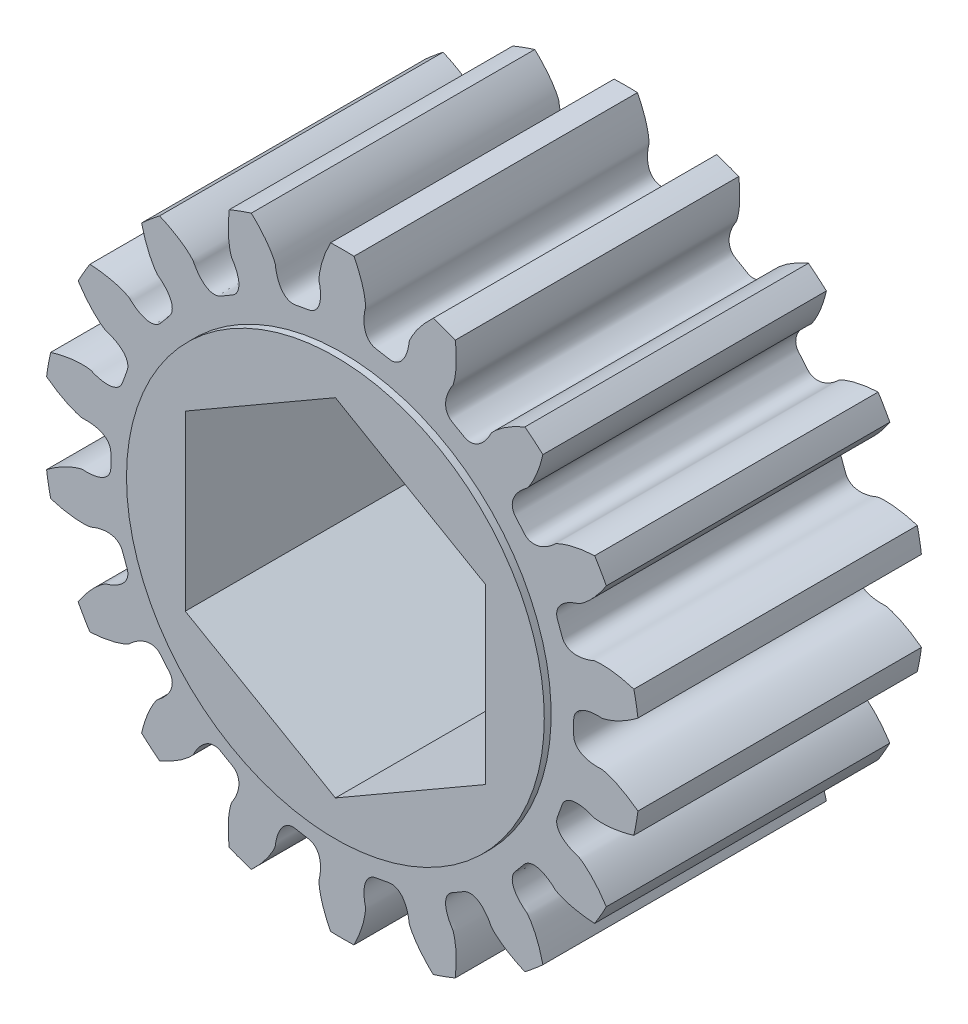
SolidWorks part; units mm, degrees
material "7075-T6 (SN)"
ref_plane "Front Plane" through (0, 0, 0) normal (0, 0, 1) x (1, 0, 0)
ref_plane "Top Plane" through (0, 0, 0) normal (0, 1, 0) x (1, 0, 0)
ref_plane "Right Plane" through (0, 0, 0) normal (1, 0, 0) x (0, 0, -1)
ref_plane "Plane1" through (0, 0, 6.0325) normal (0, 0, 1) x (1, 0, 0)
sketch "Sketch1" plane through (0, 0, 6.0325) normal (0, 0, 1) x (1, 0, 0)
  arc A0 (12.411, -2.694) -> (12.5839, -1.7132) centre (0, 0) ccw
  arc A1 (12.5839, 1.7132) -> (12.411, 2.694) centre (0, 0) ccw
  arc A2 (11.239, 5.9139) -> (10.7411, 6.7764) centre (0, 0) ccw
  arc A3 (8.5386, 9.4012) -> (7.7757, 10.0414) centre (0, 0) ccw
  arc A4 (4.8082, 11.7546) -> (3.8724, 12.0952) centre (0, 0) ccw
  arc A5 (0.498, 12.6902) -> (-0.498, 12.6902) centre (0, 0) ccw
  arc A6 (-3.8724, 12.0952) -> (-4.8082, 11.7546) centre (0, 0) ccw
  arc A7 (-7.7757, 10.0414) -> (-8.5386, 9.4012) centre (0, 0) ccw
  arc A8 (-10.7411, 6.7764) -> (-11.239, 5.9139) centre (0, 0) ccw
  arc A9 (-12.411, 2.694) -> (-12.5839, 1.7132) centre (0, 0) ccw
  arc A10 (-12.5839, -1.7132) -> (-12.411, -2.694) centre (0, 0) ccw
  arc A11 (-11.239, -5.9139) -> (-10.7411, -6.7764) centre (0, 0) ccw
  arc A12 (-8.5386, -9.4012) -> (-7.7757, -10.0414) centre (0, 0) ccw
  arc A13 (-4.8082, -11.7546) -> (-3.8724, -12.0952) centre (0, 0) ccw
  arc A14 (-0.498, -12.6902) -> (0.498, -12.6902) centre (0, 0) ccw
  arc A15 (3.8724, -12.0952) -> (4.8082, -11.7546) centre (0, 0) ccw
  arc A16 (7.7757, -10.0414) -> (8.5386, -9.4012) centre (0, 0) ccw
  arc A17 (10.7411, -6.7764) -> (11.239, -5.9139) centre (0, 0) ccw
  spline S0 degree 3 poles (11.239, -5.9139) (11.1509, -5.7775) (11.0298, -5.6051) (10.8706, -5.4047) (10.783, -5.3007) (10.6983, -5.2057) (10.6171, -5.1195) (10.5396, -5.0419) (10.4664, -4.9725) (10.3977, -4.911) (10.3341, -4.8571) (10.2759, -4.8106) (10.2233, -4.771) (10.1769, -4.7378) (10.1275, -4.7053) (10.0518, -4.6541) (9.95, -4.6355) (9.8549, -4.5968) (9.7835, -4.5675) (9.7159, -4.5362) (9.6517, -4.5038) (9.5908, -4.4699) (9.5333, -4.4347) (9.479, -4.3981) (9.4279, -4.3599) (9.3799, -4.3199) (9.3348, -4.2779) (9.2928, -4.2333) (9.2539, -4.1857) (9.2182, -4.1342) (9.1862, -4.078) (9.1588, -4.016) (9.1377, -3.9474) (9.125, -3.8716) (9.1237, -3.7895) (9.1359, -3.7108) (9.1798, -3.5695) (9.267, -3.3729) (9.3266, -3.1663) (9.3837, -3.0298) (9.425, -2.9616) (9.4787, -2.8996) (9.5372, -2.8497) (9.5975, -2.8107) (9.6583, -2.7808) (9.719, -2.7583) (9.7794, -2.7419) (9.8398, -2.7304) (9.9007, -2.7233) (9.9622, -2.72) (10.0247, -2.7203) (10.0884, -2.7238) (10.1535, -2.7307) (10.2202, -2.7407) (10.2886, -2.7539) (10.3586, -2.7703) (10.4305, -2.7899) (10.504, -2.8133) (10.6018, -2.8447) (10.6917, -2.8959) (10.7827, -2.9054) (10.8413, -2.9122) (10.8982, -2.9166) (10.9639, -2.9201) (11.0385, -2.9219) (11.1219, -2.9215) (11.2139, -2.9185) (11.3147, -2.9124) (11.4239, -2.9027) (11.5416, -2.889) (11.6675, -2.8706) (11.8014, -2.8472) (12.0522, -2.7961) (12.2559, -2.7418) (12.411, -2.694) knots 0 0 0 0 0.068568 0.088955 0.108106 0.126021 0.142701 0.158145 0.172354 0.185328 0.197065 0.207567 0.216834 0.224865 0.231661 0.241836 0.263156 0.274398 0.285253 0.295736 0.305862 0.315655 0.325139 0.334346 0.343315 0.352092 0.360737 0.369325 0.377945 0.38671 0.395752 0.405223 0.415278 0.426045 0.437578 0.449793 0.459544 0.5 0.540456 0.550207 0.562422 0.573955 0.584722 0.594777 0.604248 0.61329 0.622055 0.630675 0.639263 0.647908 0.656685 0.665654 0.674861 0.684345 0.694138 0.704264 0.714747 0.725602 0.736844 0.758164 0.768339 0.775135 0.783166 0.792433 0.802935 0.814672 0.827646 0.841855 0.857299 0.873979 0.891894 0.911045 0.931432 1 1 1 1
  spline S1 degree 3 poles (12.5839, -1.7132) (12.4545, -1.6153) (12.2817, -1.4946) (12.0635, -1.3608) (11.9456, -1.293) (11.8336, -1.2327) (11.7278, -1.1795) (11.6284, -1.133) (11.5359, -1.0929) (11.4503, -1.0586) (11.3721, -1.0297) (11.3015, -1.0059) (11.2385, -0.9867) (11.1836, -0.9714) (11.1261, -0.9577) (11.0374, -0.9355) (10.9354, -0.9529) (10.8328, -0.949) (10.7557, -0.9458) (10.6815, -0.9396) (10.61, -0.9311) (10.5412, -0.9201) (10.4751, -0.9067) (10.4116, -0.8909) (10.3505, -0.8724) (10.2917, -0.8513) (10.235, -0.8272) (10.1803, -0.7997) (10.1274, -0.7682) (10.0762, -0.7321) (10.027, -0.6902) (9.9801, -0.6413) (9.9367, -0.584) (9.8988, -0.5172) (9.8696, -0.4405) (9.8541, -0.3623) (9.847, -0.2145) (9.8618, 0) (9.847, 0.2145) (9.8541, 0.3623) (9.8696, 0.4405) (9.8988, 0.5172) (9.9367, 0.584) (9.9801, 0.6413) (10.027, 0.6902) (10.0762, 0.7321) (10.1274, 0.7682) (10.1803, 0.7997) (10.235, 0.8272) (10.2917, 0.8513) (10.3505, 0.8724) (10.4116, 0.8909) (10.4751, 0.9067) (10.5412, 0.9201) (10.61, 0.9311) (10.6815, 0.9396) (10.7557, 0.9458) (10.8328, 0.949) (10.9354, 0.9529) (11.0374, 0.9355) (11.1261, 0.9577) (11.1836, 0.9714) (11.2385, 0.9867) (11.3015, 1.0059) (11.3721, 1.0297) (11.4503, 1.0586) (11.5359, 1.0929) (11.6284, 1.133) (11.7278, 1.1795) (11.8336, 1.2327) (11.9456, 1.293) (12.0635, 1.3608) (12.2817, 1.4946) (12.4545, 1.6153) (12.5839, 1.7132) knots 0 0 0 0 0.068568 0.088955 0.108106 0.126021 0.142701 0.158145 0.172354 0.185328 0.197065 0.207567 0.216834 0.224865 0.231661 0.241836 0.263156 0.274398 0.285253 0.295736 0.305862 0.315655 0.325139 0.334346 0.343315 0.352092 0.360737 0.369325 0.377945 0.38671 0.395752 0.405223 0.415278 0.426045 0.437578 0.449793 0.459544 0.5 0.540456 0.550207 0.562422 0.573955 0.584722 0.594777 0.604248 0.61329 0.622055 0.630675 0.639263 0.647908 0.656685 0.665654 0.674861 0.684345 0.694138 0.704264 0.714747 0.725602 0.736844 0.758164 0.768339 0.775135 0.783166 0.792433 0.802935 0.814672 0.827646 0.841855 0.857299 0.873979 0.891894 0.911045 0.931432 1 1 1 1
  spline S2 degree 3 poles (12.411, 2.694) (12.2559, 2.7418) (12.0522, 2.7961) (11.8014, 2.8472) (11.6675, 2.8706) (11.5416, 2.889) (11.4239, 2.9027) (11.3147, 2.9124) (11.2139, 2.9185) (11.1219, 2.9215) (11.0385, 2.9219) (10.9639, 2.9201) (10.8982, 2.9166) (10.8413, 2.9122) (10.7827, 2.9054) (10.6917, 2.8959) (10.6018, 2.8447) (10.504, 2.8133) (10.4305, 2.7899) (10.3586, 2.7703) (10.2886, 2.7539) (10.2202, 2.7407) (10.1535, 2.7307) (10.0884, 2.7238) (10.0247, 2.7203) (9.9622, 2.72) (9.9007, 2.7233) (9.8398, 2.7304) (9.7794, 2.7419) (9.719, 2.7583) (9.6583, 2.7808) (9.5975, 2.8107) (9.5372, 2.8497) (9.4787, 2.8996) (9.425, 2.9616) (9.3837, 3.0298) (9.3266, 3.1663) (9.267, 3.3729) (9.1798, 3.5695) (9.1359, 3.7108) (9.1237, 3.7895) (9.125, 3.8716) (9.1377, 3.9474) (9.1588, 4.016) (9.1862, 4.078) (9.2182, 4.1342) (9.2539, 4.1857) (9.2928, 4.2333) (9.3348, 4.2779) (9.3799, 4.3199) (9.4279, 4.3599) (9.479, 4.3981) (9.5333, 4.4347) (9.5908, 4.4699) (9.6517, 4.5038) (9.7159, 4.5362) (9.7835, 4.5675) (9.8549, 4.5968) (9.95, 4.6355) (10.0518, 4.6541) (10.1275, 4.7053) (10.1769, 4.7378) (10.2233, 4.771) (10.2759, 4.8106) (10.3341, 4.8571) (10.3977, 4.911) (10.4664, 4.9725) (10.5396, 5.0419) (10.6171, 5.1195) (10.6983, 5.2057) (10.783, 5.3007) (10.8706, 5.4047) (11.0298, 5.6051) (11.1509, 5.7775) (11.239, 5.9139) knots 0 0 0 0 0.068568 0.088955 0.108106 0.126021 0.142701 0.158145 0.172354 0.185328 0.197065 0.207567 0.216834 0.224865 0.231661 0.241836 0.263156 0.274398 0.285253 0.295736 0.305862 0.315655 0.325139 0.334346 0.343315 0.352092 0.360737 0.369325 0.377945 0.38671 0.395752 0.405223 0.415278 0.426045 0.437578 0.449793 0.459544 0.5 0.540456 0.550207 0.562422 0.573955 0.584722 0.594777 0.604248 0.61329 0.622055 0.630675 0.639263 0.647908 0.656685 0.665654 0.674861 0.684345 0.694138 0.704264 0.714747 0.725602 0.736844 0.758164 0.768339 0.775135 0.783166 0.792433 0.802935 0.814672 0.827646 0.841855 0.857299 0.873979 0.891894 0.911045 0.931432 1 1 1 1
  spline S3 degree 3 poles (10.7411, 6.7764) (10.579, 6.7682) (10.369, 6.7496) (10.1159, 6.7118) (9.982, 6.688) (9.8574, 6.6622) (9.7422, 6.6349) (9.6362, 6.6066) (9.5395, 6.5779) (9.4519, 6.5492) (9.3735, 6.521) (9.304, 6.4939) (9.2434, 6.4682) (9.1915, 6.4445) (9.1387, 6.418) (9.0565, 6.3781) (8.9895, 6.2992) (8.9084, 6.2362) (8.8473, 6.1891) (8.7864, 6.1461) (8.7262, 6.1067) (8.6665, 6.0709) (8.6073, 6.0387) (8.5484, 6.01) (8.4897, 5.9848) (8.4311, 5.9632) (8.3722, 5.9453) (8.3126, 5.9312) (8.2518, 5.9212) (8.1894, 5.916) (8.1248, 5.9165) (8.0574, 5.9238) (7.9873, 5.9398) (7.9154, 5.9667) (7.8437, 6.0066) (7.7815, 6.0565) (7.6812, 6.1652) (7.5546, 6.339) (7.4054, 6.4939) (7.3157, 6.6116) (7.2774, 6.6815) (7.2505, 6.759) (7.2365, 6.8346) (7.2329, 6.9064) (7.2374, 6.974) (7.2483, 7.0377) (7.2642, 7.0983) (7.2845, 7.1563) (7.3088, 7.2126) (7.3367, 7.2675) (7.3681, 7.3215) (7.4031, 7.3749) (7.4416, 7.4279) (7.4836, 7.4806) (7.5292, 7.5332) (7.5785, 7.5857) (7.6314, 7.6382) (7.6884, 7.6901) (7.7645, 7.7591) (7.8538, 7.8113) (7.9074, 7.8854) (7.9427, 7.9328) (7.975, 7.9798) (8.0108, 8.035) (8.0497, 8.0987) (8.091, 8.1711) (8.1345, 8.2523) (8.1796, 8.3426) (8.2258, 8.442) (8.2727, 8.5508) (8.3198, 8.669) (8.3665, 8.7967) (8.4476, 9.0394) (8.5024, 9.243) (8.5386, 9.4012) knots 0 0 0 0 0.068568 0.088955 0.108106 0.126021 0.142701 0.158145 0.172354 0.185328 0.197065 0.207567 0.216834 0.224865 0.231661 0.241836 0.263156 0.274398 0.285253 0.295736 0.305862 0.315655 0.325139 0.334346 0.343315 0.352092 0.360737 0.369325 0.377945 0.38671 0.395752 0.405223 0.415278 0.426045 0.437578 0.449793 0.459544 0.5 0.540456 0.550207 0.562422 0.573955 0.584722 0.594777 0.604248 0.61329 0.622055 0.630675 0.639263 0.647908 0.656685 0.665654 0.674861 0.684345 0.694138 0.704264 0.714747 0.725602 0.736844 0.758164 0.768339 0.775135 0.783166 0.792433 0.802935 0.814672 0.827646 0.841855 0.857299 0.873979 0.891894 0.911045 0.931432 1 1 1 1
  spline S4 degree 3 poles (7.7757, 10.0414) (7.6261, 9.9783) (7.4352, 9.889) (7.2103, 9.7669) (7.0926, 9.6987) (6.9844, 9.6318) (6.8854, 9.5668) (6.7955, 9.504) (6.7144, 9.4439) (6.6419, 9.387) (6.5778, 9.3337) (6.5219, 9.2844) (6.4737, 9.2395) (6.433, 9.1996) (6.3925, 9.1566) (6.3289, 9.0909) (6.2929, 8.9939) (6.2382, 8.907) (6.197, 8.8418) (6.1544, 8.7806) (6.1113, 8.723) (6.0675, 8.6689) (6.0228, 8.6184) (5.9773, 8.5713) (5.9308, 8.5276) (5.8831, 8.4872) (5.8339, 8.4502) (5.7827, 8.4166) (5.729, 8.3865) (5.6721, 8.3602) (5.6112, 8.3385) (5.5455, 8.3223) (5.4741, 8.3134) (5.3973, 8.3141) (5.3163, 8.327) (5.2408, 8.3527) (5.1093, 8.4205) (4.9309, 8.5405) (4.7377, 8.6351) (4.6132, 8.715) (4.5533, 8.7675) (4.5016, 8.8312) (4.4626, 8.8974) (4.4346, 8.9637) (4.4157, 9.0287) (4.4041, 9.0923) (4.3984, 9.1547) (4.3976, 9.2162) (4.4012, 9.2774) (4.4086, 9.3385) (4.4197, 9.4) (4.4343, 9.4621) (4.4523, 9.5251) (4.4738, 9.589) (4.4987, 9.6541) (4.527, 9.7202) (4.5587, 9.7876) (4.5945, 9.8559) (4.6425, 9.9467) (4.7085, 10.0264) (4.7336, 10.1143) (4.7506, 10.1709) (4.7648, 10.2262) (4.7796, 10.2903) (4.7943, 10.3634) (4.8084, 10.4456) (4.8215, 10.5368) (4.833, 10.637) (4.8424, 10.7463) (4.8492, 10.8646) (4.853, 10.9917) (4.8533, 11.1277) (4.8465, 11.3836) (4.8284, 11.5935) (4.8082, 11.7546) knots 0 0 0 0 0.068568 0.088955 0.108106 0.126021 0.142701 0.158145 0.172354 0.185328 0.197065 0.207567 0.216834 0.224865 0.231661 0.241836 0.263156 0.274398 0.285253 0.295736 0.305862 0.315655 0.325139 0.334346 0.343315 0.352092 0.360737 0.369325 0.377945 0.38671 0.395752 0.405223 0.415278 0.426045 0.437578 0.449793 0.459544 0.5 0.540456 0.550207 0.562422 0.573955 0.584722 0.594777 0.604248 0.61329 0.622055 0.630675 0.639263 0.647908 0.656685 0.665654 0.674861 0.684345 0.694138 0.704264 0.714747 0.725602 0.736844 0.758164 0.768339 0.775135 0.783166 0.792433 0.802935 0.814672 0.827646 0.841855 0.857299 0.873979 0.891894 0.911045 0.931432 1 1 1 1
  spline S5 degree 3 poles (3.8724, 12.0952) (3.7534, 11.9848) (3.6046, 11.8356) (3.435, 11.644) (3.3477, 11.5396) (3.2689, 11.4398) (3.1981, 11.3448) (3.1351, 11.255) (3.0794, 11.1708) (3.0308, 11.0926) (2.9888, 11.0205) (2.9531, 10.9551) (2.9232, 10.8965) (2.8986, 10.845) (2.8752, 10.7907) (2.8379, 10.7073) (2.8373, 10.6038) (2.8157, 10.5034) (2.7992, 10.428) (2.7801, 10.356) (2.7593, 10.2871) (2.7366, 10.2213) (2.7119, 10.1586) (2.6853, 10.0987) (2.6565, 10.0418) (2.6255, 9.9875) (2.5919, 9.9359) (2.5553, 9.8868) (2.5152, 9.8401) (2.4707, 9.796) (2.4209, 9.7548) (2.3646, 9.7171) (2.3006, 9.6843) (2.2282, 9.6587) (2.1477, 9.6431) (2.068, 9.6414) (1.9212, 9.6602) (1.7125, 9.7119) (1.4986, 9.7347) (1.3543, 9.7673) (1.28, 9.7961) (1.2096, 9.8383) (1.1503, 9.8871) (1.1014, 9.9398) (1.0614, 9.9945) (1.0287, 10.0503) (1.002, 10.1069) (0.9803, 10.1645) (0.9627, 10.2231) (0.9488, 10.2832) (0.9382, 10.3447) (0.9306, 10.4081) (0.926, 10.4735) (0.9243, 10.5409) (0.9255, 10.6105) (0.9295, 10.6823) (0.9362, 10.7565) (0.9465, 10.833) (0.9605, 10.9347) (0.9953, 11.0321) (0.9888, 11.1233) (0.9854, 11.1823) (0.9799, 11.2391) (0.9719, 11.3044) (0.9607, 11.3782) (0.9458, 11.4602) (0.9269, 11.5504) (0.9034, 11.6485) (0.8749, 11.7544) (0.8409, 11.8679) (0.801, 11.9887) (0.7547, 12.1166) (0.6608, 12.3546) (0.572, 12.5458) (0.498, 12.6902) knots 0 0 0 0 0.068568 0.088955 0.108106 0.126021 0.142701 0.158145 0.172354 0.185328 0.197065 0.207567 0.216834 0.224865 0.231661 0.241836 0.263156 0.274398 0.285253 0.295736 0.305862 0.315655 0.325139 0.334346 0.343315 0.352092 0.360737 0.369325 0.377945 0.38671 0.395752 0.405223 0.415278 0.426045 0.437578 0.449793 0.459544 0.5 0.540456 0.550207 0.562422 0.573955 0.584722 0.594777 0.604248 0.61329 0.622055 0.630675 0.639263 0.647908 0.656685 0.665654 0.674861 0.684345 0.694138 0.704264 0.714747 0.725602 0.736844 0.758164 0.768339 0.775135 0.783166 0.792433 0.802935 0.814672 0.827646 0.841855 0.857299 0.873979 0.891894 0.911045 0.931432 1 1 1 1
  spline S6 degree 3 poles (-0.498, 12.6902) (-0.572, 12.5458) (-0.6608, 12.3546) (-0.7547, 12.1166) (-0.801, 11.9887) (-0.8409, 11.8679) (-0.8749, 11.7544) (-0.9034, 11.6485) (-0.9269, 11.5504) (-0.9458, 11.4602) (-0.9607, 11.3782) (-0.9719, 11.3044) (-0.9799, 11.2391) (-0.9854, 11.1823) (-0.9888, 11.1233) (-0.9953, 11.0321) (-0.9605, 10.9347) (-0.9465, 10.833) (-0.9362, 10.7565) (-0.9295, 10.6823) (-0.9255, 10.6105) (-0.9243, 10.5409) (-0.926, 10.4735) (-0.9306, 10.4081) (-0.9382, 10.3447) (-0.9488, 10.2832) (-0.9627, 10.2231) (-0.9803, 10.1645) (-1.002, 10.1069) (-1.0287, 10.0503) (-1.0614, 9.9945) (-1.1014, 9.9398) (-1.1503, 9.8871) (-1.2096, 9.8383) (-1.28, 9.7961) (-1.3543, 9.7673) (-1.4986, 9.7347) (-1.7125, 9.7119) (-1.9212, 9.6602) (-2.068, 9.6414) (-2.1477, 9.6431) (-2.2282, 9.6587) (-2.3006, 9.6843) (-2.3646, 9.7171) (-2.4209, 9.7548) (-2.4707, 9.796) (-2.5152, 9.8401) (-2.5553, 9.8868) (-2.5919, 9.9359) (-2.6255, 9.9875) (-2.6565, 10.0418) (-2.6853, 10.0987) (-2.7119, 10.1586) (-2.7366, 10.2213) (-2.7593, 10.2871) (-2.7801, 10.356) (-2.7992, 10.428) (-2.8157, 10.5034) (-2.8373, 10.6038) (-2.8379, 10.7073) (-2.8752, 10.7907) (-2.8986, 10.845) (-2.9232, 10.8965) (-2.9531, 10.9551) (-2.9888, 11.0205) (-3.0308, 11.0926) (-3.0794, 11.1708) (-3.1351, 11.255) (-3.1981, 11.3448) (-3.2689, 11.4398) (-3.3477, 11.5396) (-3.435, 11.644) (-3.6046, 11.8356) (-3.7534, 11.9848) (-3.8724, 12.0952) knots 0 0 0 0 0.068568 0.088955 0.108106 0.126021 0.142701 0.158145 0.172354 0.185328 0.197065 0.207567 0.216834 0.224865 0.231661 0.241836 0.263156 0.274398 0.285253 0.295736 0.305862 0.315655 0.325139 0.334346 0.343315 0.352092 0.360737 0.369325 0.377945 0.38671 0.395752 0.405223 0.415278 0.426045 0.437578 0.449793 0.459544 0.5 0.540456 0.550207 0.562422 0.573955 0.584722 0.594777 0.604248 0.61329 0.622055 0.630675 0.639263 0.647908 0.656685 0.665654 0.674861 0.684345 0.694138 0.704264 0.714747 0.725602 0.736844 0.758164 0.768339 0.775135 0.783166 0.792433 0.802935 0.814672 0.827646 0.841855 0.857299 0.873979 0.891894 0.911045 0.931432 1 1 1 1
  spline S7 degree 3 poles (-4.8082, 11.7546) (-4.8284, 11.5935) (-4.8465, 11.3836) (-4.8533, 11.1277) (-4.853, 10.9917) (-4.8492, 10.8646) (-4.8424, 10.7463) (-4.833, 10.637) (-4.8215, 10.5368) (-4.8084, 10.4456) (-4.7943, 10.3634) (-4.7796, 10.2903) (-4.7648, 10.2262) (-4.7506, 10.1709) (-4.7336, 10.1143) (-4.7085, 10.0264) (-4.6425, 9.9467) (-4.5945, 9.8559) (-4.5587, 9.7876) (-4.527, 9.7202) (-4.4987, 9.6541) (-4.4738, 9.589) (-4.4523, 9.5251) (-4.4343, 9.4621) (-4.4197, 9.4) (-4.4086, 9.3385) (-4.4012, 9.2774) (-4.3976, 9.2162) (-4.3984, 9.1547) (-4.4041, 9.0923) (-4.4157, 9.0287) (-4.4346, 8.9637) (-4.4626, 8.8974) (-4.5016, 8.8312) (-4.5533, 8.7675) (-4.6132, 8.715) (-4.7377, 8.6351) (-4.9309, 8.5405) (-5.1093, 8.4205) (-5.2408, 8.3527) (-5.3163, 8.327) (-5.3973, 8.3141) (-5.4741, 8.3134) (-5.5455, 8.3223) (-5.6112, 8.3385) (-5.6721, 8.3602) (-5.729, 8.3865) (-5.7827, 8.4166) (-5.8339, 8.4502) (-5.8831, 8.4872) (-5.9308, 8.5276) (-5.9773, 8.5713) (-6.0228, 8.6184) (-6.0675, 8.6689) (-6.1113, 8.723) (-6.1544, 8.7806) (-6.197, 8.8418) (-6.2382, 8.907) (-6.2929, 8.9939) (-6.3289, 9.0909) (-6.3925, 9.1566) (-6.433, 9.1996) (-6.4737, 9.2395) (-6.5219, 9.2844) (-6.5778, 9.3337) (-6.6419, 9.387) (-6.7144, 9.4439) (-6.7954, 9.504) (-6.8854, 9.5668) (-6.9844, 9.6318) (-7.0926, 9.6987) (-7.2103, 9.7669) (-7.4352, 9.889) (-7.6261, 9.9783) (-7.7757, 10.0414) knots 0 0 0 0 0.068568 0.088955 0.108106 0.126021 0.142701 0.158145 0.172354 0.185328 0.197065 0.207567 0.216834 0.224865 0.231661 0.241836 0.263156 0.274398 0.285253 0.295736 0.305862 0.315655 0.325139 0.334346 0.343315 0.352092 0.360737 0.369325 0.377945 0.38671 0.395752 0.405223 0.415278 0.426045 0.437578 0.449793 0.459544 0.5 0.540456 0.550207 0.562422 0.573955 0.584722 0.594777 0.604248 0.61329 0.622055 0.630675 0.639263 0.647908 0.656685 0.665654 0.674861 0.684345 0.694138 0.704264 0.714747 0.725602 0.736844 0.758164 0.768339 0.775135 0.783166 0.792433 0.802935 0.814672 0.827646 0.841855 0.857299 0.873979 0.891894 0.911045 0.931432 1 1 1 1
  spline S8 degree 3 poles (-8.5386, 9.4012) (-8.5024, 9.243) (-8.4476, 9.0394) (-8.3665, 8.7967) (-8.3198, 8.669) (-8.2727, 8.5508) (-8.2258, 8.442) (-8.1796, 8.3426) (-8.1345, 8.2523) (-8.091, 8.1711) (-8.0497, 8.0987) (-8.0108, 8.035) (-7.975, 7.9798) (-7.9427, 7.9328) (-7.9074, 7.8854) (-7.8538, 7.8113) (-7.7645, 7.7591) (-7.6884, 7.6901) (-7.6314, 7.6382) (-7.5785, 7.5857) (-7.5292, 7.5332) (-7.4836, 7.4806) (-7.4416, 7.4279) (-7.4031, 7.3749) (-7.3681, 7.3215) (-7.3367, 7.2675) (-7.3088, 7.2126) (-7.2845, 7.1563) (-7.2642, 7.0983) (-7.2483, 7.0377) (-7.2374, 6.974) (-7.2329, 6.9064) (-7.2365, 6.8346) (-7.2505, 6.759) (-7.2774, 6.6815) (-7.3157, 6.6116) (-7.4054, 6.4939) (-7.5546, 6.339) (-7.6812, 6.1652) (-7.7815, 6.0565) (-7.8437, 6.0066) (-7.9154, 5.9667) (-7.9873, 5.9398) (-8.0574, 5.9238) (-8.1248, 5.9165) (-8.1894, 5.916) (-8.2518, 5.9212) (-8.3126, 5.9312) (-8.3722, 5.9453) (-8.4311, 5.9632) (-8.4897, 5.9848) (-8.5484, 6.01) (-8.6073, 6.0387) (-8.6665, 6.0709) (-8.7262, 6.1067) (-8.7864, 6.1461) (-8.8473, 6.1891) (-8.9084, 6.2362) (-8.9895, 6.2992) (-9.0565, 6.3781) (-9.1387, 6.418) (-9.1915, 6.4445) (-9.2434, 6.4682) (-9.304, 6.4939) (-9.3735, 6.521) (-9.4519, 6.5492) (-9.5395, 6.5779) (-9.6362, 6.6066) (-9.7422, 6.6349) (-9.8574, 6.6622) (-9.982, 6.688) (-10.1159, 6.7118) (-10.369, 6.7496) (-10.579, 6.7682) (-10.7411, 6.7764) knots 0 0 0 0 0.068568 0.088955 0.108106 0.126021 0.142701 0.158145 0.172354 0.185328 0.197065 0.207567 0.216834 0.224865 0.231661 0.241836 0.263156 0.274398 0.285253 0.295736 0.305862 0.315655 0.325139 0.334346 0.343315 0.352092 0.360737 0.369325 0.377945 0.38671 0.395752 0.405223 0.415278 0.426045 0.437578 0.449793 0.459544 0.5 0.540456 0.550207 0.562422 0.573955 0.584722 0.594777 0.604248 0.61329 0.622055 0.630675 0.639263 0.647908 0.656685 0.665654 0.674861 0.684345 0.694138 0.704264 0.714747 0.725602 0.736844 0.758164 0.768339 0.775135 0.783166 0.792433 0.802935 0.814672 0.827646 0.841855 0.857299 0.873979 0.891894 0.911045 0.931432 1 1 1 1
  spline S9 degree 3 poles (-11.239, 5.9139) (-11.1509, 5.7775) (-11.0298, 5.6051) (-10.8706, 5.4047) (-10.783, 5.3007) (-10.6983, 5.2057) (-10.6171, 5.1195) (-10.5396, 5.0419) (-10.4664, 4.9725) (-10.3977, 4.911) (-10.3341, 4.8571) (-10.2759, 4.8106) (-10.2233, 4.771) (-10.1769, 4.7378) (-10.1275, 4.7053) (-10.0518, 4.6541) (-9.95, 4.6355) (-9.8549, 4.5968) (-9.7835, 4.5675) (-9.7159, 4.5362) (-9.6517, 4.5038) (-9.5908, 4.4699) (-9.5333, 4.4347) (-9.479, 4.3981) (-9.4279, 4.3599) (-9.3799, 4.3199) (-9.3348, 4.2779) (-9.2928, 4.2333) (-9.2539, 4.1857) (-9.2182, 4.1342) (-9.1862, 4.078) (-9.1588, 4.016) (-9.1377, 3.9474) (-9.125, 3.8716) (-9.1237, 3.7895) (-9.1359, 3.7108) (-9.1798, 3.5695) (-9.267, 3.3729) (-9.3266, 3.1663) (-9.3837, 3.0298) (-9.425, 2.9616) (-9.4787, 2.8996) (-9.5372, 2.8497) (-9.5975, 2.8107) (-9.6583, 2.7808) (-9.719, 2.7583) (-9.7794, 2.7419) (-9.8398, 2.7304) (-9.9007, 2.7233) (-9.9622, 2.72) (-10.0247, 2.7203) (-10.0884, 2.7238) (-10.1535, 2.7307) (-10.2202, 2.7407) (-10.2886, 2.7539) (-10.3586, 2.7703) (-10.4305, 2.7899) (-10.504, 2.8133) (-10.6018, 2.8447) (-10.6917, 2.8959) (-10.7827, 2.9054) (-10.8413, 2.9122) (-10.8982, 2.9166) (-10.9639, 2.9201) (-11.0385, 2.9219) (-11.1219, 2.9215) (-11.2139, 2.9185) (-11.3147, 2.9124) (-11.4239, 2.9027) (-11.5416, 2.889) (-11.6675, 2.8706) (-11.8014, 2.8472) (-12.0522, 2.7961) (-12.2559, 2.7418) (-12.411, 2.694) knots 0 0 0 0 0.068568 0.088955 0.108106 0.126021 0.142701 0.158145 0.172354 0.185328 0.197065 0.207567 0.216834 0.224865 0.231661 0.241836 0.263156 0.274398 0.285253 0.295736 0.305862 0.315655 0.325139 0.334346 0.343315 0.352092 0.360737 0.369325 0.377945 0.38671 0.395752 0.405223 0.415278 0.426045 0.437578 0.449793 0.459544 0.5 0.540456 0.550207 0.562422 0.573955 0.584722 0.594777 0.604248 0.61329 0.622055 0.630675 0.639263 0.647908 0.656685 0.665654 0.674861 0.684345 0.694138 0.704264 0.714747 0.725602 0.736844 0.758164 0.768339 0.775135 0.783166 0.792433 0.802935 0.814672 0.827646 0.841855 0.857299 0.873979 0.891894 0.911045 0.931432 1 1 1 1
  spline S10 degree 3 poles (-12.5839, 1.7132) (-12.4545, 1.6153) (-12.2817, 1.4946) (-12.0635, 1.3608) (-11.9456, 1.293) (-11.8336, 1.2327) (-11.7278, 1.1795) (-11.6284, 1.133) (-11.5359, 1.0929) (-11.4503, 1.0586) (-11.3721, 1.0297) (-11.3015, 1.0059) (-11.2385, 0.9867) (-11.1836, 0.9714) (-11.1261, 0.9577) (-11.0374, 0.9355) (-10.9354, 0.9529) (-10.8328, 0.949) (-10.7557, 0.9458) (-10.6815, 0.9396) (-10.61, 0.9311) (-10.5412, 0.9201) (-10.4751, 0.9067) (-10.4116, 0.8909) (-10.3505, 0.8724) (-10.2917, 0.8513) (-10.235, 0.8272) (-10.1803, 0.7997) (-10.1274, 0.7682) (-10.0762, 0.7321) (-10.027, 0.6902) (-9.9801, 0.6413) (-9.9367, 0.584) (-9.8988, 0.5172) (-9.8696, 0.4405) (-9.8541, 0.3623) (-9.847, 0.2145) (-9.8618, 0) (-9.847, -0.2145) (-9.8541, -0.3623) (-9.8696, -0.4405) (-9.8988, -0.5172) (-9.9367, -0.584) (-9.9801, -0.6413) (-10.027, -0.6902) (-10.0762, -0.7321) (-10.1274, -0.7682) (-10.1803, -0.7997) (-10.235, -0.8272) (-10.2917, -0.8513) (-10.3505, -0.8724) (-10.4116, -0.8909) (-10.4751, -0.9067) (-10.5412, -0.9201) (-10.61, -0.9311) (-10.6815, -0.9396) (-10.7557, -0.9458) (-10.8328, -0.949) (-10.9354, -0.9529) (-11.0374, -0.9355) (-11.1261, -0.9577) (-11.1836, -0.9714) (-11.2385, -0.9867) (-11.3015, -1.0059) (-11.3721, -1.0297) (-11.4503, -1.0586) (-11.5359, -1.0929) (-11.6284, -1.133) (-11.7278, -1.1795) (-11.8336, -1.2327) (-11.9456, -1.293) (-12.0635, -1.3608) (-12.2817, -1.4946) (-12.4545, -1.6153) (-12.5839, -1.7132) knots 0 0 0 0 0.068568 0.088955 0.108106 0.126021 0.142701 0.158145 0.172354 0.185328 0.197065 0.207567 0.216834 0.224865 0.231661 0.241836 0.263156 0.274398 0.285253 0.295736 0.305862 0.315655 0.325139 0.334346 0.343315 0.352092 0.360737 0.369325 0.377945 0.38671 0.395752 0.405223 0.415278 0.426045 0.437578 0.449793 0.459544 0.5 0.540456 0.550207 0.562422 0.573955 0.584722 0.594777 0.604248 0.61329 0.622055 0.630675 0.639263 0.647908 0.656685 0.665654 0.674861 0.684345 0.694138 0.704264 0.714747 0.725602 0.736844 0.758164 0.768339 0.775135 0.783166 0.792433 0.802935 0.814672 0.827646 0.841855 0.857299 0.873979 0.891894 0.911045 0.931432 1 1 1 1
  spline S11 degree 3 poles (-12.411, -2.694) (-12.2559, -2.7418) (-12.0522, -2.7961) (-11.8014, -2.8472) (-11.6675, -2.8706) (-11.5416, -2.889) (-11.4239, -2.9027) (-11.3147, -2.9124) (-11.2139, -2.9185) (-11.1219, -2.9215) (-11.0385, -2.9219) (-10.9639, -2.9201) (-10.8982, -2.9166) (-10.8413, -2.9122) (-10.7827, -2.9054) (-10.6917, -2.8959) (-10.6018, -2.8447) (-10.504, -2.8133) (-10.4305, -2.7899) (-10.3586, -2.7703) (-10.2886, -2.7539) (-10.2202, -2.7407) (-10.1535, -2.7307) (-10.0884, -2.7238) (-10.0247, -2.7203) (-9.9622, -2.72) (-9.9007, -2.7233) (-9.8398, -2.7304) (-9.7794, -2.7419) (-9.719, -2.7583) (-9.6583, -2.7808) (-9.5975, -2.8107) (-9.5372, -2.8497) (-9.4787, -2.8996) (-9.425, -2.9616) (-9.3837, -3.0298) (-9.3266, -3.1663) (-9.267, -3.3729) (-9.1798, -3.5695) (-9.1359, -3.7108) (-9.1237, -3.7895) (-9.125, -3.8716) (-9.1377, -3.9474) (-9.1588, -4.016) (-9.1862, -4.078) (-9.2182, -4.1342) (-9.2539, -4.1857) (-9.2928, -4.2333) (-9.3348, -4.2779) (-9.3799, -4.3199) (-9.4279, -4.3599) (-9.479, -4.3981) (-9.5333, -4.4347) (-9.5908, -4.4699) (-9.6517, -4.5038) (-9.7159, -4.5362) (-9.7835, -4.5675) (-9.8549, -4.5968) (-9.95, -4.6355) (-10.0518, -4.6541) (-10.1275, -4.7053) (-10.1769, -4.7378) (-10.2233, -4.771) (-10.2759, -4.8106) (-10.3341, -4.8571) (-10.3977, -4.911) (-10.4664, -4.9725) (-10.5396, -5.0419) (-10.6171, -5.1195) (-10.6983, -5.2057) (-10.783, -5.3007) (-10.8706, -5.4047) (-11.0298, -5.6051) (-11.1509, -5.7775) (-11.239, -5.9139) knots 0 0 0 0 0.068568 0.088955 0.108106 0.126021 0.142701 0.158145 0.172354 0.185328 0.197065 0.207567 0.216834 0.224865 0.231661 0.241836 0.263156 0.274398 0.285253 0.295736 0.305862 0.315655 0.325139 0.334346 0.343315 0.352092 0.360737 0.369325 0.377945 0.38671 0.395752 0.405223 0.415278 0.426045 0.437578 0.449793 0.459544 0.5 0.540456 0.550207 0.562422 0.573955 0.584722 0.594777 0.604248 0.61329 0.622055 0.630675 0.639263 0.647908 0.656685 0.665654 0.674861 0.684345 0.694138 0.704264 0.714747 0.725602 0.736844 0.758164 0.768339 0.775135 0.783166 0.792433 0.802935 0.814672 0.827646 0.841855 0.857299 0.873979 0.891894 0.911045 0.931432 1 1 1 1
  spline S12 degree 3 poles (-10.7411, -6.7764) (-10.579, -6.7682) (-10.369, -6.7496) (-10.1159, -6.7118) (-9.982, -6.688) (-9.8574, -6.6622) (-9.7422, -6.6349) (-9.6362, -6.6066) (-9.5395, -6.5779) (-9.4519, -6.5492) (-9.3735, -6.521) (-9.304, -6.4939) (-9.2434, -6.4682) (-9.1915, -6.4445) (-9.1387, -6.418) (-9.0565, -6.3781) (-8.9895, -6.2992) (-8.9084, -6.2362) (-8.8473, -6.1891) (-8.7864, -6.1461) (-8.7262, -6.1067) (-8.6665, -6.0709) (-8.6073, -6.0387) (-8.5484, -6.01) (-8.4897, -5.9848) (-8.4311, -5.9632) (-8.3722, -5.9453) (-8.3126, -5.9312) (-8.2518, -5.9212) (-8.1894, -5.916) (-8.1248, -5.9165) (-8.0574, -5.9238) (-7.9873, -5.9398) (-7.9154, -5.9667) (-7.8437, -6.0066) (-7.7815, -6.0565) (-7.6812, -6.1652) (-7.5546, -6.339) (-7.4054, -6.4939) (-7.3157, -6.6116) (-7.2774, -6.6815) (-7.2505, -6.759) (-7.2365, -6.8346) (-7.2329, -6.9064) (-7.2374, -6.974) (-7.2483, -7.0377) (-7.2642, -7.0983) (-7.2845, -7.1563) (-7.3088, -7.2126) (-7.3367, -7.2675) (-7.3681, -7.3215) (-7.4031, -7.3749) (-7.4416, -7.4279) (-7.4836, -7.4806) (-7.5292, -7.5332) (-7.5785, -7.5857) (-7.6314, -7.6382) (-7.6884, -7.6901) (-7.7645, -7.7591) (-7.8538, -7.8113) (-7.9074, -7.8854) (-7.9427, -7.9328) (-7.975, -7.9798) (-8.0108, -8.035) (-8.0497, -8.0987) (-8.091, -8.1711) (-8.1345, -8.2523) (-8.1796, -8.3426) (-8.2258, -8.442) (-8.2727, -8.5508) (-8.3198, -8.669) (-8.3665, -8.7967) (-8.4476, -9.0394) (-8.5024, -9.243) (-8.5386, -9.4012) knots 0 0 0 0 0.068568 0.088955 0.108106 0.126021 0.142701 0.158145 0.172354 0.185328 0.197065 0.207567 0.216834 0.224865 0.231661 0.241836 0.263156 0.274398 0.285253 0.295736 0.305862 0.315655 0.325139 0.334346 0.343315 0.352092 0.360737 0.369325 0.377945 0.38671 0.395752 0.405223 0.415278 0.426045 0.437578 0.449793 0.459544 0.5 0.540456 0.550207 0.562422 0.573955 0.584722 0.594777 0.604248 0.61329 0.622055 0.630675 0.639263 0.647908 0.656685 0.665654 0.674861 0.684345 0.694138 0.704264 0.714747 0.725602 0.736844 0.758164 0.768339 0.775135 0.783166 0.792433 0.802935 0.814672 0.827646 0.841855 0.857299 0.873979 0.891894 0.911045 0.931432 1 1 1 1
  spline S13 degree 3 poles (-7.7757, -10.0414) (-7.6261, -9.9783) (-7.4352, -9.889) (-7.2103, -9.7669) (-7.0926, -9.6987) (-6.9844, -9.6318) (-6.8854, -9.5668) (-6.7954, -9.504) (-6.7144, -9.4439) (-6.6419, -9.387) (-6.5778, -9.3337) (-6.5219, -9.2844) (-6.4737, -9.2395) (-6.433, -9.1996) (-6.3925, -9.1566) (-6.3289, -9.0909) (-6.2929, -8.9939) (-6.2382, -8.907) (-6.197, -8.8418) (-6.1544, -8.7806) (-6.1113, -8.723) (-6.0675, -8.6689) (-6.0228, -8.6184) (-5.9773, -8.5713) (-5.9308, -8.5276) (-5.8831, -8.4872) (-5.8339, -8.4502) (-5.7827, -8.4166) (-5.729, -8.3865) (-5.6721, -8.3602) (-5.6112, -8.3385) (-5.5455, -8.3223) (-5.4741, -8.3134) (-5.3973, -8.3141) (-5.3163, -8.327) (-5.2408, -8.3527) (-5.1093, -8.4205) (-4.9309, -8.5405) (-4.7377, -8.6351) (-4.6132, -8.715) (-4.5533, -8.7675) (-4.5016, -8.8312) (-4.4626, -8.8974) (-4.4346, -8.9637) (-4.4157, -9.0287) (-4.4041, -9.0923) (-4.3984, -9.1547) (-4.3976, -9.2162) (-4.4012, -9.2774) (-4.4086, -9.3385) (-4.4197, -9.4) (-4.4343, -9.4621) (-4.4523, -9.5251) (-4.4738, -9.589) (-4.4987, -9.6541) (-4.527, -9.7202) (-4.5587, -9.7876) (-4.5945, -9.8559) (-4.6425, -9.9467) (-4.7085, -10.0264) (-4.7336, -10.1143) (-4.7506, -10.1709) (-4.7648, -10.2262) (-4.7796, -10.2903) (-4.7943, -10.3634) (-4.8084, -10.4456) (-4.8215, -10.5368) (-4.833, -10.637) (-4.8424, -10.7463) (-4.8492, -10.8646) (-4.853, -10.9917) (-4.8533, -11.1277) (-4.8465, -11.3836) (-4.8284, -11.5935) (-4.8082, -11.7546) knots 0 0 0 0 0.068568 0.088955 0.108106 0.126021 0.142701 0.158145 0.172354 0.185328 0.197065 0.207567 0.216834 0.224865 0.231661 0.241836 0.263156 0.274398 0.285253 0.295736 0.305862 0.315655 0.325139 0.334346 0.343315 0.352092 0.360737 0.369325 0.377945 0.38671 0.395752 0.405223 0.415278 0.426045 0.437578 0.449793 0.459544 0.5 0.540456 0.550207 0.562422 0.573955 0.584722 0.594777 0.604248 0.61329 0.622055 0.630675 0.639263 0.647908 0.656685 0.665654 0.674861 0.684345 0.694138 0.704264 0.714747 0.725602 0.736844 0.758164 0.768339 0.775135 0.783166 0.792433 0.802935 0.814672 0.827646 0.841855 0.857299 0.873979 0.891894 0.911045 0.931432 1 1 1 1
  spline S14 degree 3 poles (-3.8724, -12.0952) (-3.7534, -11.9848) (-3.6046, -11.8356) (-3.435, -11.644) (-3.3477, -11.5396) (-3.2689, -11.4398) (-3.1981, -11.3448) (-3.1351, -11.255) (-3.0794, -11.1708) (-3.0308, -11.0926) (-2.9888, -11.0205) (-2.9531, -10.9551) (-2.9232, -10.8965) (-2.8986, -10.845) (-2.8752, -10.7907) (-2.8379, -10.7073) (-2.8373, -10.6038) (-2.8157, -10.5034) (-2.7992, -10.428) (-2.7801, -10.356) (-2.7593, -10.2871) (-2.7366, -10.2213) (-2.7119, -10.1586) (-2.6853, -10.0987) (-2.6565, -10.0418) (-2.6255, -9.9875) (-2.5919, -9.9359) (-2.5553, -9.8868) (-2.5152, -9.8401) (-2.4707, -9.796) (-2.4209, -9.7548) (-2.3646, -9.7171) (-2.3006, -9.6843) (-2.2282, -9.6587) (-2.1477, -9.6431) (-2.068, -9.6414) (-1.9212, -9.6602) (-1.7125, -9.7119) (-1.4986, -9.7347) (-1.3543, -9.7673) (-1.28, -9.7961) (-1.2096, -9.8383) (-1.1503, -9.8871) (-1.1014, -9.9398) (-1.0614, -9.9945) (-1.0287, -10.0503) (-1.002, -10.1069) (-0.9803, -10.1645) (-0.9627, -10.2231) (-0.9488, -10.2832) (-0.9382, -10.3447) (-0.9306, -10.4081) (-0.926, -10.4735) (-0.9243, -10.5409) (-0.9255, -10.6105) (-0.9295, -10.6823) (-0.9362, -10.7565) (-0.9465, -10.833) (-0.9605, -10.9347) (-0.9953, -11.0321) (-0.9888, -11.1233) (-0.9854, -11.1823) (-0.9799, -11.2391) (-0.9719, -11.3044) (-0.9607, -11.3782) (-0.9458, -11.4602) (-0.9269, -11.5504) (-0.9034, -11.6485) (-0.8749, -11.7544) (-0.8409, -11.8679) (-0.801, -11.9887) (-0.7547, -12.1166) (-0.6608, -12.3546) (-0.572, -12.5458) (-0.498, -12.6902) knots 0 0 0 0 0.068568 0.088955 0.108106 0.126021 0.142701 0.158145 0.172354 0.185328 0.197065 0.207567 0.216834 0.224865 0.231661 0.241836 0.263156 0.274398 0.285253 0.295736 0.305862 0.315655 0.325139 0.334346 0.343315 0.352092 0.360737 0.369325 0.377945 0.38671 0.395752 0.405223 0.415278 0.426045 0.437578 0.449793 0.459544 0.5 0.540456 0.550207 0.562422 0.573955 0.584722 0.594777 0.604248 0.61329 0.622055 0.630675 0.639263 0.647908 0.656685 0.665654 0.674861 0.684345 0.694138 0.704264 0.714747 0.725602 0.736844 0.758164 0.768339 0.775135 0.783166 0.792433 0.802935 0.814672 0.827646 0.841855 0.857299 0.873979 0.891894 0.911045 0.931432 1 1 1 1
  spline S15 degree 3 poles (0.498, -12.6902) (0.572, -12.5458) (0.6608, -12.3546) (0.7547, -12.1166) (0.801, -11.9887) (0.8409, -11.8679) (0.8749, -11.7544) (0.9034, -11.6485) (0.9269, -11.5504) (0.9458, -11.4602) (0.9607, -11.3782) (0.9719, -11.3044) (0.9799, -11.2391) (0.9854, -11.1823) (0.9888, -11.1233) (0.9953, -11.0321) (0.9605, -10.9347) (0.9465, -10.833) (0.9362, -10.7565) (0.9295, -10.6823) (0.9255, -10.6105) (0.9243, -10.5409) (0.926, -10.4735) (0.9306, -10.4081) (0.9382, -10.3447) (0.9488, -10.2832) (0.9627, -10.2231) (0.9803, -10.1645) (1.002, -10.1069) (1.0287, -10.0503) (1.0614, -9.9945) (1.1014, -9.9398) (1.1503, -9.8871) (1.2096, -9.8383) (1.28, -9.7961) (1.3543, -9.7673) (1.4986, -9.7347) (1.7125, -9.7119) (1.9212, -9.6602) (2.068, -9.6414) (2.1477, -9.6431) (2.2282, -9.6587) (2.3006, -9.6843) (2.3646, -9.7171) (2.4209, -9.7548) (2.4707, -9.796) (2.5152, -9.8401) (2.5553, -9.8868) (2.5919, -9.9359) (2.6255, -9.9875) (2.6565, -10.0418) (2.6853, -10.0987) (2.7119, -10.1586) (2.7366, -10.2213) (2.7593, -10.2871) (2.7801, -10.356) (2.7992, -10.428) (2.8157, -10.5034) (2.8373, -10.6038) (2.8379, -10.7073) (2.8752, -10.7907) (2.8986, -10.845) (2.9232, -10.8965) (2.9531, -10.9551) (2.9888, -11.0205) (3.0308, -11.0926) (3.0794, -11.1708) (3.1351, -11.255) (3.1981, -11.3448) (3.2689, -11.4398) (3.3477, -11.5396) (3.435, -11.644) (3.6046, -11.8356) (3.7534, -11.9848) (3.8724, -12.0952) knots 0 0 0 0 0.068568 0.088955 0.108106 0.126021 0.142701 0.158145 0.172354 0.185328 0.197065 0.207567 0.216834 0.224865 0.231661 0.241836 0.263156 0.274398 0.285253 0.295736 0.305862 0.315655 0.325139 0.334346 0.343315 0.352092 0.360737 0.369325 0.377945 0.38671 0.395752 0.405223 0.415278 0.426045 0.437578 0.449793 0.459544 0.5 0.540456 0.550207 0.562422 0.573955 0.584722 0.594777 0.604248 0.61329 0.622055 0.630675 0.639263 0.647908 0.656685 0.665654 0.674861 0.684345 0.694138 0.704264 0.714747 0.725602 0.736844 0.758164 0.768339 0.775135 0.783166 0.792433 0.802935 0.814672 0.827646 0.841855 0.857299 0.873979 0.891894 0.911045 0.931432 1 1 1 1
  spline S16 degree 3 poles (4.8082, -11.7546) (4.8284, -11.5935) (4.8465, -11.3836) (4.8533, -11.1277) (4.853, -10.9917) (4.8492, -10.8646) (4.8424, -10.7463) (4.833, -10.637) (4.8215, -10.5368) (4.8084, -10.4456) (4.7943, -10.3634) (4.7796, -10.2903) (4.7648, -10.2262) (4.7506, -10.1709) (4.7336, -10.1143) (4.7085, -10.0264) (4.6425, -9.9467) (4.5945, -9.8559) (4.5587, -9.7876) (4.527, -9.7202) (4.4987, -9.6541) (4.4738, -9.589) (4.4523, -9.5251) (4.4343, -9.4621) (4.4197, -9.4) (4.4086, -9.3385) (4.4012, -9.2774) (4.3976, -9.2162) (4.3984, -9.1547) (4.4041, -9.0923) (4.4157, -9.0287) (4.4346, -8.9637) (4.4626, -8.8974) (4.5016, -8.8312) (4.5533, -8.7675) (4.6132, -8.715) (4.7377, -8.6351) (4.9309, -8.5405) (5.1093, -8.4205) (5.2408, -8.3527) (5.3163, -8.327) (5.3973, -8.3141) (5.4741, -8.3134) (5.5455, -8.3223) (5.6112, -8.3385) (5.6721, -8.3602) (5.729, -8.3865) (5.7827, -8.4166) (5.8339, -8.4502) (5.8831, -8.4872) (5.9308, -8.5276) (5.9773, -8.5713) (6.0228, -8.6184) (6.0675, -8.6689) (6.1113, -8.723) (6.1544, -8.7806) (6.197, -8.8418) (6.2382, -8.907) (6.2929, -8.9939) (6.3289, -9.0909) (6.3925, -9.1566) (6.433, -9.1996) (6.4737, -9.2395) (6.5219, -9.2844) (6.5778, -9.3337) (6.6419, -9.387) (6.7144, -9.4439) (6.7955, -9.504) (6.8854, -9.5668) (6.9844, -9.6318) (7.0926, -9.6987) (7.2103, -9.7669) (7.4352, -9.889) (7.6261, -9.9783) (7.7757, -10.0414) knots 0 0 0 0 0.068568 0.088955 0.108106 0.126021 0.142701 0.158145 0.172354 0.185328 0.197065 0.207567 0.216834 0.224865 0.231661 0.241836 0.263156 0.274398 0.285253 0.295736 0.305862 0.315655 0.325139 0.334346 0.343315 0.352092 0.360737 0.369325 0.377945 0.38671 0.395752 0.405223 0.415278 0.426045 0.437578 0.449793 0.459544 0.5 0.540456 0.550207 0.562422 0.573955 0.584722 0.594777 0.604248 0.61329 0.622055 0.630675 0.639263 0.647908 0.656685 0.665654 0.674861 0.684345 0.694138 0.704264 0.714747 0.725602 0.736844 0.758164 0.768339 0.775135 0.783166 0.792433 0.802935 0.814672 0.827646 0.841855 0.857299 0.873979 0.891894 0.911045 0.931432 1 1 1 1
  spline S17 degree 3 poles (8.5386, -9.4012) (8.5024, -9.243) (8.4476, -9.0394) (8.3665, -8.7967) (8.3198, -8.669) (8.2727, -8.5508) (8.2258, -8.442) (8.1796, -8.3426) (8.1345, -8.2523) (8.091, -8.1711) (8.0497, -8.0987) (8.0108, -8.035) (7.975, -7.9798) (7.9427, -7.9328) (7.9074, -7.8854) (7.8538, -7.8113) (7.7645, -7.7591) (7.6884, -7.6901) (7.6314, -7.6382) (7.5785, -7.5857) (7.5292, -7.5332) (7.4836, -7.4806) (7.4416, -7.4279) (7.4031, -7.3749) (7.3681, -7.3215) (7.3367, -7.2675) (7.3088, -7.2126) (7.2845, -7.1563) (7.2642, -7.0983) (7.2483, -7.0377) (7.2374, -6.974) (7.2329, -6.9064) (7.2365, -6.8346) (7.2505, -6.759) (7.2774, -6.6815) (7.3157, -6.6116) (7.4054, -6.4939) (7.5546, -6.339) (7.6812, -6.1652) (7.7815, -6.0565) (7.8437, -6.0066) (7.9154, -5.9667) (7.9873, -5.9398) (8.0574, -5.9238) (8.1248, -5.9165) (8.1894, -5.916) (8.2518, -5.9212) (8.3126, -5.9312) (8.3722, -5.9453) (8.4311, -5.9632) (8.4897, -5.9848) (8.5484, -6.01) (8.6073, -6.0387) (8.6665, -6.0709) (8.7262, -6.1067) (8.7864, -6.1461) (8.8473, -6.1891) (8.9084, -6.2362) (8.9895, -6.2992) (9.0565, -6.3781) (9.1387, -6.418) (9.1915, -6.4445) (9.2434, -6.4682) (9.304, -6.4939) (9.3735, -6.521) (9.4519, -6.5492) (9.5395, -6.5779) (9.6362, -6.6066) (9.7422, -6.6349) (9.8574, -6.6622) (9.982, -6.688) (10.1159, -6.7118) (10.369, -6.7496) (10.579, -6.7682) (10.7411, -6.7764) knots 0 0 0 0 0.068568 0.088955 0.108106 0.126021 0.142701 0.158145 0.172354 0.185328 0.197065 0.207567 0.216834 0.224865 0.231661 0.241836 0.263156 0.274398 0.285253 0.295736 0.305862 0.315655 0.325139 0.334346 0.343315 0.352092 0.360737 0.369325 0.377945 0.38671 0.395752 0.405223 0.415278 0.426045 0.437578 0.449793 0.459544 0.5 0.540456 0.550207 0.562422 0.573955 0.584722 0.594777 0.604248 0.61329 0.622055 0.630675 0.639263 0.647908 0.656685 0.665654 0.674861 0.684345 0.694138 0.704264 0.714747 0.725602 0.736844 0.758164 0.768339 0.775135 0.783166 0.792433 0.802935 0.814672 0.827646 0.841855 0.857299 0.873979 0.891894 0.911045 0.931432 1 1 1 1
extrude "Boss-Extrude1" add sketch "Sketch1" against normal blind 12.065
sketch "Sketch2" plane through (0, 0, 6.0325) normal (0, 0, 1) x (1, 0, 0)
  circle A0 centre (0, 0) radius 8.89
extrude "Boss-Extrude2" add sketch "Sketch2" along normal blind 0.2921
sketch "Sketch3" plane through (0, 0, -6.0325) normal (0, 0, -1) x (-1, 0, 0)
  circle A0 centre (0, 0) radius 8.89
extrude "Boss-Extrude3" add sketch "Sketch3" along normal blind 0.2921
sketch "Sketch4" plane through (0, 0, -6.3246) normal (0, 0, -1) x (-1, 0, 0)
  line L0 (0, -7.3763) -> (6.3881, -3.6882)
  line L1 (6.3881, -3.6882) -> (6.3881, 3.6882)
  line L2 (6.3881, 3.6882) -> (0, 7.3763)
  line L3 (0, 7.3763) -> (-6.3881, 3.6882)
  line L4 (-6.3881, 3.6882) -> (-6.3881, -3.6882)
  line L5 (-6.3881, -3.6882) -> (0, -7.3763)
extrude "Cut-Extrude1" cut sketch "Sketch4" against normal through all
